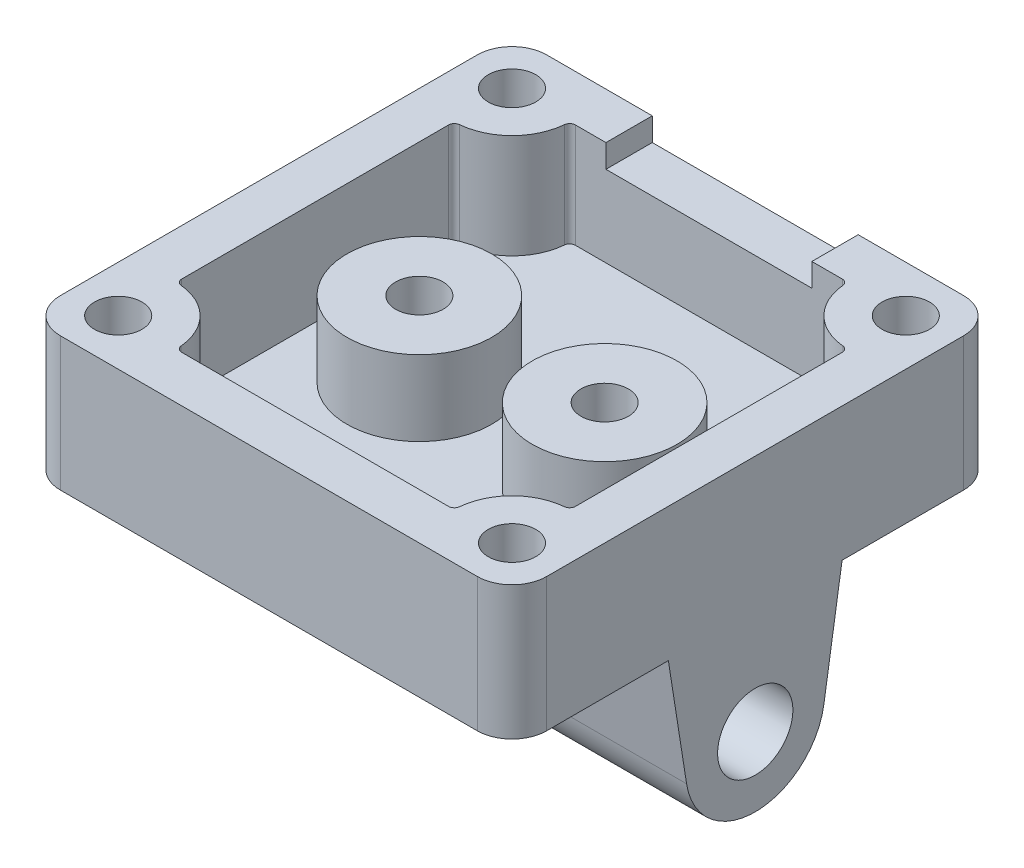
SolidWorks part; units mm, degrees
material "ABS"
ref_plane "Front Plane" through (0, 0, 0) normal (0, 0, 1) x (1, 0, 0)
ref_plane "Top Plane" through (0, 0, 0) normal (0, 1, 0) x (1, 0, 0)
ref_plane "Right Plane" through (0, 0, 0) normal (1, 0, 0) x (0, 0, -1)
sketch "Sketch1" plane through (0, 0, 0) normal (0, 1, 0) x (1, 0, 0)
  line L1 (-21, 21) -> (21, 21)
  line L2 (-21, 21) -> (-21, -21)
  line L3 (-21, -21) -> (21, -21)
  line L4 (21, 21) -> (21, -21)
  line L5 (-21, 21) -> (21, -21) construction
  line L6 (-21, -21) -> (21, 21) construction
  point P0 (0, 0)
  dimension "D1" = 42
  dimension "D2" = 42
extrude "Boss-Extrude1" add sketch "Sketch1" along normal blind 2.54
sketch "Sketch2" plane through (0, 2.54, 0) normal (0, 1, 0) x (1, 0, 0)
  line L26 (-21, 21) -> (21, 21)
  line L44 (-21, 21) -> (-21, -21)
  line L45 (-21, -21) -> (21, -21)
  line L49 (21, 21) -> (21, -21)
  line L50 (-21, 21) -> (21, -21) construction
  line L51 (-21, -21) -> (21, 21) construction
  line L55 (-17, 11.5228) -> (-17, -11.5228)
  line L56 (-11.5228, -17) -> (11.5228, -17)
  line L57 (17, 11.5228) -> (17, -11.5228)
  line L58 (-11.5228, 17) -> (11.5228, 17)
  line L63 (-17, 17) -> (-17, -17) construction
  line L64 (-17, -17) -> (17, -17) construction
  line L65 (17, 17) -> (17, -17) construction
  line L66 (-17, 17) -> (17, 17) construction
  line L68 (-13.4645, 13.4645) -> (13.4645, 13.4645) construction
  line L69 (-13.4645, 13.4645) -> (-13.4645, -13.4645) construction
  line L70 (-13.4645, -13.4645) -> (13.4645, -13.4645) construction
  line L71 (13.4645, 13.4645) -> (13.4645, -13.4645) construction
  line L72 (-13.4645, 13.4645) -> (13.4645, -13.4645) construction
  line L73 (-13.4645, -13.4645) -> (13.4645, 13.4645) construction
  arc A0 (-16.5455, -12.0207) -> (-12.0207, -16.5455) centre (-17, -17) cw
  arc A2 (12.0207, -16.5455) -> (16.5455, -12.0207) centre (17, -17) cw
  arc A4 (16.5455, 12.0207) -> (12.0207, 16.5455) centre (17, 17) cw
  arc A6 (-12.0207, 16.5455) -> (-16.5455, 12.0207) centre (-17, 17) cw
  arc A8 (-16.5455, -12.0207) -> (-17, -11.5228) centre (-16.5, -11.5228) cw
  arc A9 (-12.0207, -16.5455) -> (-11.5228, -17) centre (-11.5228, -16.5) ccw
  arc A10 (12.0207, -16.5455) -> (11.5228, -17) centre (11.5228, -16.5) cw
  arc A11 (16.5455, -12.0207) -> (17, -11.5228) centre (16.5, -11.5228) ccw
  arc A12 (16.5455, 12.0207) -> (17, 11.5228) centre (16.5, 11.5228) cw
  arc A13 (12.0207, 16.5455) -> (11.5228, 17) centre (11.5228, 16.5) ccw
  arc A14 (-12.0207, 16.5455) -> (-11.5228, 17) centre (-11.5228, 16.5) cw
  arc A15 (-16.5455, 12.0207) -> (-17, 11.5228) centre (-16.5, 11.5228) ccw
  point P0 (0, 0)
  point P44 (0, 0)
  dimension "D2" = 5
  dimension "D3" = 0.5
  dimension "D1" = 4
  dimension "D4" = 26.9289
  dimension "D5" = 26.9289
extrude "Boss-Extrude2" add sketch "Sketch2" along normal blind 9
sketch "Sketch4" plane through (-21, 0, 0) normal (-1, 0, 0) x (0, 0, 1)
  line L0 (7.5, 0) -> (5.9271, -10)
  line L1 (-21, 0) -> (21, 0) construction
  line L2 (-5.9271, -10) -> (-7.5, 0)
  line L3 (7.5, 0) -> (-7.5, 0)
  arc A0 (5.9271, -10) -> (-5.9271, -10) centre (0, -9.0677) cw
  circle A1 centre (0, -9.0677) radius 3.25
  point P11 (0, 0)
  point P12 (0, 0)
  dimension "D1" = 6.5
  dimension "D4" = 6
  dimension "D2" = 10
  dimension "D3" = 15
extrude "Boss-Extrude4" add sketch "Sketch4" against normal up to surface (42 mm away) up to face at (21, 5.77, 0)
mirror "Mirror1" [suppressed] about plane through (0, 0, 0) normal (1, 0, 0)
sketch "Sketch9" plane through (0, 2.54, 0) normal (0, 1, 0) x (1, 0, 0)
  line L0 (0, -1.397) -> (0, 1.397) construction
  line L1 (0, 0) -> (-8, 0) construction
  circle A0 centre (8, 0) radius 2.05
  circle A1 centre (8, 0) radius 6.25
  circle A2 centre (-8, 0) radius 6.25
  circle A3 centre (-8, 0) radius 2.05
  dimension "D1" = 4.1
  dimension "D2" = 4.2
  dimension "D3" = 8
extrude "Boss-Extrude5" add sketch "Sketch9" along normal blind 6.5
sketch "Sketch10" plane through (0, 11.54, 0) normal (0, 1, 0) x (1, 0, 0)
  circle A0 centre (-17, 17) radius 2.05
  circle A1 centre (17, 17) radius 2.05
  circle A2 centre (-17, -17) radius 2.05
  circle A3 centre (17, -17) radius 2.05
  dimension "D1" = 4.1
extrude "Cut-Extrude1" cut sketch "Sketch10" against normal blind 8
sketch "Sketch12" plane through (0, 0, -21) normal (0, 0, -1) x (-1, 0, 0)
  line L0 (-21, 11.54) -> (21, 11.54) construction
  line L1 (8.89, 9.54) -> (-8.89, 9.54)
  line L2 (8.89, 9.54) -> (8.89, 11.54)
  line L3 (8.89, 11.54) -> (-8.89, 11.54)
  line L4 (-8.89, 9.54) -> (-8.89, 11.54)
  line L5 (8.89, 9.54) -> (-8.89, 11.54) construction
  line L6 (8.89, 11.54) -> (-8.89, 9.54) construction
  point P0 (0, 10.54)
  point P7 (0, 11.54)
  point P8 (0, 11.54)
  dimension "D1" = 2
  dimension "D2" = 17.78
extrude "Cut-Extrude2" cut sketch "Sketch12" against normal up to surface (4 mm away) up to face at (0, 7.04, -17)
fillet "Fillet1" radius 3 4 edges at (21, 5.77, 21) (-21, 5.77, 21) (-21, 5.77, -21) (21, 5.77, -21)
